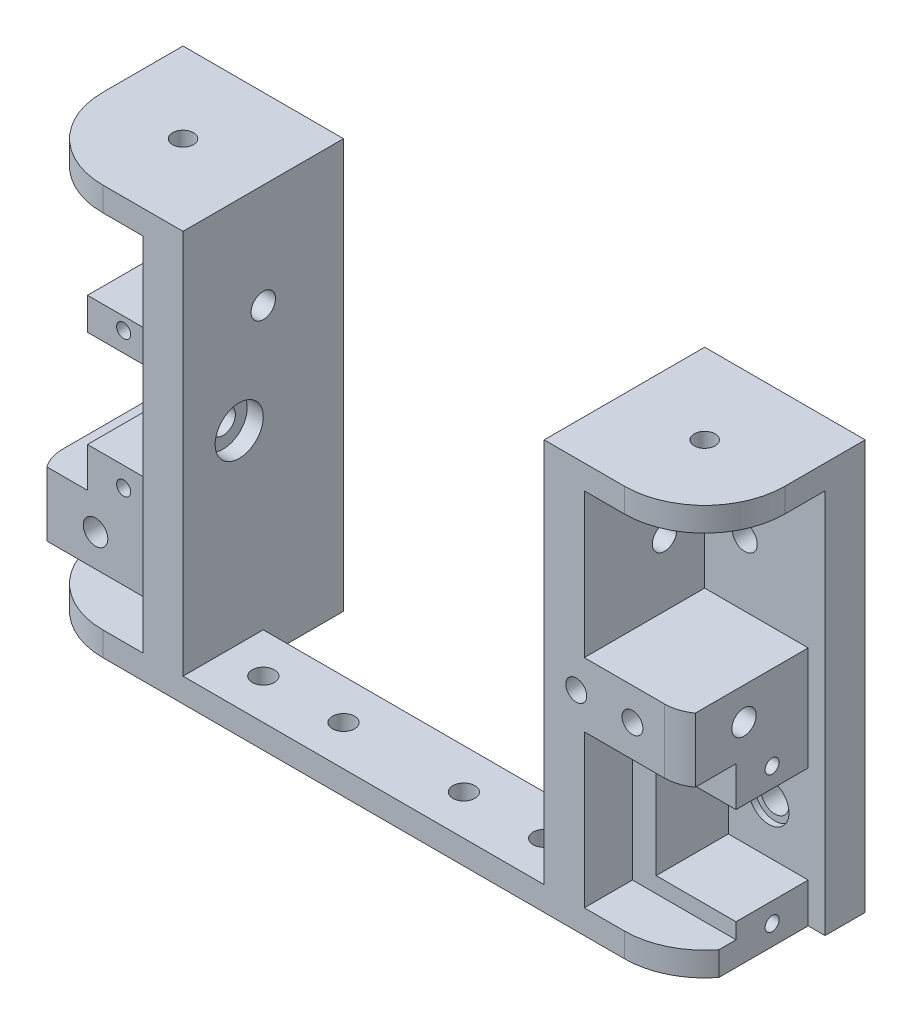
SolidWorks part; units mm, degrees
material "ABS"
ref_plane "Front Plane" through (0, 0, 0) normal (0, 0, 1) x (1, 0, 0)
ref_plane "Top Plane" through (0, 0, 0) normal (0, 1, 0) x (1, 0, 0)
ref_plane "Right Plane" through (0, 0, 0) normal (1, 0, 0) x (0, 0, -1)
sketch "Sketch1" plane through (0, 0, 0) normal (0, 0, 1) x (1, 0, 0)
  line L0 (-22.5, 7) -> (0, 7)
  line L1 (22.5, 7) -> (22.5, 45)
  line L2 (22.5, 45) -> (42.5, 45)
  line L3 (42.5, 45) -> (42.5, 0)
  line L4 (42.5, 0) -> (-42.5, 0)
  line L5 (-42.5, 0) -> (-42.5, 45)
  line L6 (-42.5, 45) -> (-22.5, 45)
  line L7 (-22.5, 45) -> (-22.5, 7)
  line L8 (-35.5, 39.9194) -> (-35.5, 0) construction
  line L9 (35.5, 39.9194) -> (35.5, 0) construction
  line L10 (0, 7) -> (0, 0) construction
  line L14 (0, 7) -> (22.5, 7)
  circle A0 centre (35.5, 8) radius 1.75
  circle A1 centre (-35.5, 8) radius 1.525
  circle A2 centre (32.5, 35) radius 1.55
  circle A3 centre (-32.5, 35) radius 1.55
  point P8 (0, 0)
  dimension "D3" = 3.5
  dimension "D10" = 3.1
  dimension "D11" = 3.05
  dimension "D1" = 71
  dimension "D2" = 22.5
  dimension "D4" = 8
  dimension "D5" = 7
  dimension "D6" = 7
  dimension "D7" = 45
  dimension "D8" = 35
  dimension "D9" = 3
extrude "main flange" add sketch "Sketch1" along normal blind 5
ref_plane "Plane1" through (22.5, 0, 0) normal (1, 0, 0) x (0, 0, -1)
sketch "Sketch2" plane through (22.5, 0, 0) normal (1, 0, 0) x (0, 0, -1)
  line L0 (-13, 45) -> (-13, 0) construction
  line L1 (-5, 45) -> (-20, 45)
  line L2 (-5, 45) -> (-5, 0)
  line L3 (-5, 0) -> (-20, 0)
  line L4 (-20, 45) -> (-20, 0)
  circle A0 centre (-13, 23) radius 1.525
  circle A1 centre (-10, 35) radius 1.525
  dimension "D2" = 3.05
  dimension "D5" = 3.05
  dimension "D1" = 15
  dimension "D3" = 23
  dimension "D4" = 13
  dimension "D6" = 35
  dimension "D7" = 3
extrude "side flange" add sketch "Sketch2" along normal blind 5
sketch "Sketch8" plane through (22.5, 0, 0) normal (-1, 0, 0) x (0, 0, 1)
  circle A0 centre (13, 23) radius 3
  dimension "D1" = 6
extrude "bearing cutout" [suppressed] cut sketch "Sketch8" against normal blind 2
mirror "Mirror1" about plane through (0, 0, 0) normal (1, 0, 0) of "side flange"
sketch "Sketch11" plane through (0, 0, 0) normal (0, -1, 0) x (1, 0, 0)
  line L0 (27.5, 20) -> (22.5, 20) construction
  line L1 (-42.5, 0) -> (42.5, 0)
  line L2 (-42.5, 0) -> (-42.5, 10)
  line L3 (-32.5, 20) -> (32.5, 20)
  line L4 (42.5, 0) -> (42.5, 10)
  arc A0 (32.5, 20) -> (42.5, 10) centre (32.5, 10) cw
  arc A1 (-42.5, 10) -> (-32.5, 20) centre (-32.5, 10) cw
  circle A2 centre (-32.5, 10) radius 1.3
  circle A3 centre (32.5, 10) radius 1.3
  dimension "D1" = 10
  dimension "D2" = 2.6
extrude "Boss-Extrude3" add sketch "Sketch11" along normal blind 3
sketch "Sketch12" plane through (0, 0, 0) normal (0, 1, 0) x (1, 0, 0)
  line L0 (-4, -3) -> (-4, 0)
  line L1 (22.5, 0) -> (-22.5, 0) construction
  line L2 (-4, 0) -> (4, 0)
  line L3 (4, 0) -> (4, -3)
  line L4 (0, 0) -> (0, -3) construction
  arc A0 (4, -3) -> (-4, -3) centre (0, -3) cw
  circle A1 centre (0, -3) radius 1.5 construction
  dimension "D2" = 8
  dimension "D3" = 3
  dimension "D1" = 3
extrude "Boss-Extrude4" add sketch "Sketch12" along normal up to surface (7 mm away) up to face at (5.625, 7, 3.125)
hole_wizard "CSK for M3 Flat Head Machine Screw1" positions "Sketch14" profile "Sketch15" countersink size "M3" standard "ANSI Metric" end condition up to next
sketch "Sketch14" plane through (0, -3, 0) normal (0, -1, 0) x (-1, 0, 0)
  line L0 (0, -3) -> (0, 0) construction
  point P0 (0, -3)
  dimension "D1" = 3
sketch "Sketch15" plane through (0, -3, 3) normal (1, 0, 0) x (0, 0, -1)
  line L0 (0, 0) -> (0, 10)
  line L1 (0, 10) -> (1.8, 10)
  line L2 (1.8, 10) -> (1.8, 1.5)
  line L3 (1.8, 1.5) -> (3.15, 0.15)
  line L4 (3.15, 0.15) -> (3.15, 0)
  line L6 (3.15, 0) -> (0, 0)
  line L7 (-1.8, 1.5) -> (-3.15, 0.15) construction
  line L11 (0, -6.35) -> (0, 107.95) construction
  dimension "Thru Hole Dia." = 3.6
  dimension "Thru Hole Depth" = 10
  dimension "C'Sink Dia." = 6.3
  dimension "C'Sink Angle" = 90
  dimension "Head Clearance" = 0.15
sketch "Sketch16" plane through (0, 45, 0) normal (0, 1, 0) x (1, 0, 0)
  line L0 (-22.5, 0) -> (-42.5, 0) construction
  line L1 (-42.5, 0) -> (-22.5, 0)
  line L2 (-42.5, 0) -> (-42.5, -10)
  line L3 (-32.5, -20) -> (-22.5, -20)
  line L4 (42.5, 0) -> (42.5, -10)
  line L5 (-42.5, -5) -> (-42.5, 0) construction
  line L6 (42.5, -5) -> (42.5, 0) construction
  line L7 (27.5, -20) -> (22.5, -20) construction
  line L8 (-22.5, 0) -> (-22.5, -20)
  line L9 (-22.5, -20) -> (-22.5, 0) construction
  line L10 (22.5, 0) -> (22.5, -20)
  line L11 (22.5, -20) -> (22.5, 0) construction
  line L12 (22.5, 0) -> (42.5, 0)
  line L13 (22.5, -20) -> (32.5, -20)
  arc A0 (-42.5, -10) -> (-32.5, -20) centre (-32.5, -10) ccw
  arc A1 (32.5, -20) -> (42.5, -10) centre (32.5, -10) ccw
  circle A2 centre (-32.5, -10) radius 1.3
  circle A3 centre (32.5, -10) radius 1.3
  dimension "D1" = 10
  dimension "D2" = 2.6
extrude "Top support" add sketch "Sketch16" along normal blind 3
sketch "Sketch18" plane through (27.5, 0, 0) normal (1, 0, 0) x (0, 0, -1)
  line L0 (-20, 45) -> (-20, 0) construction
  line L1 (-20, 27) -> (-5, 27)
  line L2 (-20, 27) -> (-20, 19)
  line L3 (-20, 19) -> (-5, 19)
  line L4 (-5, 27) -> (-5, 19)
  line L5 (-5, 0) -> (-5, 45) construction
  circle A0 centre (-13, 23) radius 1.525
  circle A1 centre (-13, 23) radius 1.525 construction
  dimension "D1" = 4
  dimension "D2" = 4
extrude "Boss-Extrude5" add sketch "Sketch18" along normal up to surface (15 mm away) up to face at (42.5, 19.6875, 5.9375)
sketch "Sketch19" plane through (0, 0, 5) normal (0, 0, 1) x (1, 0, 0)
  line L0 (-27.5, 45) -> (-27.5, 0) construction
  line L1 (-27.5, 12) -> (-42.5, 12)
  line L2 (-27.5, 12) -> (-27.5, 4)
  line L3 (-27.5, 4) -> (-42.5, 4)
  line L4 (-42.5, 12) -> (-42.5, 4)
  line L5 (-42.5, 45) -> (-42.5, 0) construction
  circle A0 centre (-35.5, 8) radius 1.525
  circle A1 centre (-35.5, 8) radius 1.525 construction
  dimension "D1" = 4
  dimension "D2" = 4
extrude "Boss-Extrude6" add sketch "Sketch19" along normal up to surface (15 mm away) up to face at (8.375, 27.35, 20)
fillet "Fillet1" radius 5 2 edges at (42.5, 23, 20) (-42.5, 8, 20)
hole_wizard "M3x0.5 Tapped Hole1" positions "Sketch21" profile "Sketch20" tap size "M3x0.5" standard "ANSI Metric"
sketch "Sketch21" plane through (-42.5, 0, 0) normal (-1, 0, 0) x (0, 0, 1)
  line L2 (15, 8) -> (4, 8) construction
  line L3 (0, 48) -> (0, -3) construction
  line L5 (15, 4) -> (15, 12) construction
  point P0 (11, 8)
  point P11 (4, 8)
  dimension "D1" = 4
  dimension "D3" = 7
sketch "Sketch20" plane through (-42.5, 8, 11) normal (0, 1, 0) x (0, 0, 1)
  line L0 (0, 0) -> (0, 8.2811)
  line L1 (0, 8.2811) -> (1.3, 7.5)
  line L2 (1.3, 7.5) -> (1.3, 0)
  line L5 (1.3, 0) -> (0, 0)
  line L10 (0, 8.2811) -> (-1.3, 7.5) construction
  line L11 (0, -6.35) -> (0, 107.95) construction
  dimension "Tap Drill Dia." = 2.6
  dimension "Tap Drill Depth" = 7.5
  dimension "Drill Angle" = 118
cosmetic thread "Hole Thread1" parameters "D1"=6, "D2"=3
cosmetic thread "Hole Thread2" parameters "D1"=6, "D2"=3
hole_wizard "M3x0.5 Tapped Hole2" positions "Sketch23" profile "Sketch22" tap size "M3x0.5" standard "ANSI Metric"
sketch "Sketch23" plane through (0, 0, 20) normal (0, 0, 1) x (1, 0, 0)
  line L0 (22.5, 23) -> (33.5, 23) construction
  line L1 (22.5, 48) -> (22.5, 0) construction
  line L5 (33.5, 23) -> (37.5, 23) construction
  line L6 (37.5, 19) -> (37.5, 27) construction
  point P0 (33.5, 23)
  point P2 (26.5, 23)
  dimension "D1" = 4
  dimension "D2" = 7
sketch "Sketch22" plane through (33.5, 23, 20) normal (1, 0, 0) x (0, -1, 0)
  line L0 (0, 0) -> (0, 8.2811)
  line L1 (0, 8.2811) -> (1.3, 7.5)
  line L2 (1.3, 7.5) -> (1.3, 0)
  line L5 (1.3, 0) -> (0, 0)
  line L10 (0, 8.2811) -> (-1.3, 7.5) construction
  line L11 (0, -6.35) -> (0, 107.95) construction
  dimension "Tap Drill Dia." = 2.6
  dimension "Tap Drill Depth" = 7.5
  dimension "Drill Angle" = 118
cosmetic thread "Hole Thread3" parameters "D1"=6, "D2"=3
cosmetic thread "Hole Thread4" parameters "D1"=6, "D2"=3
sketch "Sketch24" plane through (0, 0, 5) normal (0, 0, 1) x (1, 0, 0)
  circle A0 centre (35.5, 8) radius 2.5
  dimension "D1" = 5
extrude "Cut-Extrude1" cut sketch "Sketch24" against normal blind 0.75
sketch "Sketch25" plane through (-27.5, 0, 0) normal (-1, 0, 0) x (0, 0, 1)
  circle A0 centre (13, 23) radius 2.5
  dimension "D1" = 5
extrude "Cut-Extrude2" cut sketch "Sketch25" against normal blind 0.75
sketch "Sketch26" plane through (0, 7, 0) normal (0, 1, 0) x (1, 0, 0)
  line L0 (22.5, 0) -> (-22.5, 0) construction
  line L1 (-15.2, 0) -> (-5.2, 0)
  line L2 (-15.2, 0) -> (-15.2, -2.85)
  line L3 (-15.2, -2.85) -> (-5.2, -2.85)
  line L4 (-5.2, 0) -> (-5.2, -2.85)
  line L5 (0, 0) -> (0, 9.323) construction
  line L6 (5.2, 0) -> (5.2, -2.85)
  line L7 (15.2, -2.85) -> (5.2, -2.85)
  line L8 (15.2, 0) -> (15.2, -2.85)
  line L9 (15.2, 0) -> (5.2, 0)
  dimension "D1" = 5.2
  dimension "D2" = 2.85
  dimension "D3" = 10
extrude "Boss-Extrude7" add sketch "Sketch26" along normal blind 10
sketch "Sketch27" plane through (0, 0, 5) normal (0, 0, 1) x (1, 0, 0)
  line L0 (-27.5, 45) -> (-27.5, 12) construction
  line L1 (-27.5, 38) -> (-42.5, 38)
  line L2 (-27.5, 38) -> (-27.5, 32)
  line L3 (-27.5, 32) -> (-42.5, 32)
  line L4 (-42.5, 38) -> (-42.5, 32)
  line L5 (-42.5, 45) -> (-42.5, 12) construction
  line L6 (0, 0) -> (0, 39.7852) construction
  line L7 (-42.5, 35) -> (-32.5, 35) construction
  line L8 (42.5, 35) -> (32.5, 35) construction
  line L9 (42.5, 38) -> (42.5, 32)
  line L10 (27.5, 32) -> (42.5, 32)
  line L11 (27.5, 38) -> (27.5, 32)
  line L12 (27.5, 38) -> (42.5, 38)
  dimension "D1" = 6
sketch "Sketch30" plane through (0, 0, 0) normal (0, 1, 0) x (1, 0, 0)
  line L0 (-22.5, -20) -> (-22.5, -5) construction
  line L1 (-22.5, -5) -> (-3.4641, -5) construction
  line L2 (3.4641, -5) -> (22.5, -5) construction
  line L3 (22.5, -20) -> (22.5, -5) construction
  line L4 (22.5, -20) -> (-22.5, -20) construction
  line L5 (-22.5, -20) -> (-22.5, -5)
  line L6 (-22.5, -5) -> (-3.4641, -5)
  line L7 (3.4641, -5) -> (22.5, -5)
  line L8 (22.5, -20) -> (22.5, -5)
  line L9 (22.5, -20) -> (-22.5, -20)
  arc A0 (-3.4641, -5) -> (3.4641, -5) centre (0, -3) ccw construction
  arc A1 (-3.4641, -5) -> (3.4641, -5) centre (0, -3) ccw
extrude "Cut-Extrude3" [suppressed] cut sketch "Sketch30" against normal offset from surface (2 mm away) 1
sketch "Sketch31" [suppressed] plane through (0, 7, 0) normal (0, 1, 0) x (1, 0, 0)
  line L0 (22.5, -11) -> (22.5, 11) construction
  line L1 (-15.2, 0) -> (-22.5, 0)
  line L2 (-15.2, 0) -> (-15.2, -5)
  line L3 (-15.2, -5) -> (-22.5, -5)
  line L4 (-22.5, 0) -> (-22.5, -5)
  line L5 (15.2, 0) -> (22.5, 0)
  line L6 (15.2, 0) -> (15.2, -5)
  line L7 (15.2, -5) -> (22.5, -5)
  line L8 (22.5, 0) -> (22.5, -5)
  line L9 (3.4641, -5) -> (22.5, -5) construction
extrude "Cut-Extrude4" [suppressed] cut sketch "Sketch31" against normal blind 7
sketch "Sketch32" plane through (0, 0, 5) normal (0, 0, 1) x (1, 0, 0)
  line L0 (40.4, 14.05) -> (30.45, 14.05)
  line L2 (30.45, 14.05) -> (30.45, 1.95)
  line L3 (30.45, 1.95) -> (40.4, 1.95)
  line L4 (40.4, 1.95) -> (40.4, 0)
  line L5 (40.4, 0) -> (27.5, 0)
  line L6 (27.5, 0) -> (27.5, 19) construction
  line L7 (27.5, 0) -> (42.5, 0) construction
  line L8 (27.5, 0) -> (27.5, 19)
  line L9 (27.5, 19) -> (40.4, 19)
  line L10 (40.4, 19) -> (40.4, 14.05)
  line L11 (35.5, 8) -> (30.45, 8) construction
  line L12 (37.5, 19) -> (27.5, 19) construction
  dimension "D1" = 12.1
  dimension "D2" = 5.05
  dimension "D3" = 4.9
extrude "Motor mount" add sketch "Sketch32" along normal blind 9
sketch "Sketch33" plane through (42.5, 0, 0) normal (1, 0, 0) x (0, 0, -1)
  line L0 (-15, 27) -> (-5, 27) construction
  line L1 (-20, -3) -> (-5, -3)
  line L2 (-20, -3) -> (-20, 27)
  line L3 (-20, 27) -> (-5, 27)
  line L4 (-5, -3) -> (-5, 27)
  line L5 (-20, -3) -> (-5, 27) construction
  line L6 (-20, 27) -> (-5, -3) construction
  line L7 (-5, 0) -> (-5, 19) construction
  line L8 (0, -3) -> (-10, -3) construction
  line L9 (-20, 19) -> (-20, 27) construction
  point P0 (-12.5, 12)
extrude "Cut-Extrude6" cut sketch "Sketch33" against normal up to surface (2.1 mm away) up to face at (40.4, 16.525, 9.5)
sketch "Sketch34" plane through (40.4, 0, 0) normal (1, 0, 0) x (0, 0, -1)
  line L0 (-9.5, 16.5) -> (-9.5, 14.05) construction
  line L1 (-14, 14.05) -> (-5, 14.05) construction
  line L2 (-9.5, 14.05) -> (-9.5, 1.95) construction
  line L3 (-14, 1.95) -> (-5, 1.95) construction
  line L4 (-9.5, 1.95) -> (-9.5, -3) construction
  line L5 (-16.1311, -3) -> (-5, -3) construction
  line L7 (-9.5, 8) -> (-14.7798, 8) construction
  circle A0 centre (-9.5, 16.5) radius 0.875
  circle A1 centre (-9.5, -0.5) radius 0.875
  dimension "D1" = 1.75
  dimension "D2" = 17
  dimension "D3" = 8.5
extrude "Cut-Extrude7" cut sketch "Sketch34" against normal blind 7
sketch "Sketch35" plane through (-27.5, 0, 0) normal (-1, 0, 0) x (0, 0, 1)
  line L0 (13, 23) -> (20, 23) construction
  line L1 (20, 45) -> (20, 12) construction
  line L2 (20, 29.05) -> (7.95, 29.05)
  line L3 (7.95, 29.05) -> (7.95, 16.95)
  line L4 (7.95, 16.95) -> (20, 16.95)
  line L5 (20, 16.95) -> (20, 12)
  line L6 (20, 12) -> (5, 12)
  line L7 (5, 12) -> (5, 33.05)
  line L8 (5, 33.05) -> (20, 33.05)
  line L9 (20, 33.05) -> (20, 29.05)
  line L10 (13, 23) -> (7.95, 23) construction
  dimension "D1" = 5.05
  dimension "D2" = 12.1
  dimension "D3" = 4
extrude "Boss-Extrude9" add sketch "Sketch35" along normal blind 9
sketch "Sketch36" plane through (0, 0, 20) normal (0, 0, 1) x (1, 0, 0)
  line L0 (-42.5, 45) -> (-42.5, 12) construction
  line L1 (-27.5, 33.05) -> (-42.5, 33.05)
  line L2 (-27.5, 33.05) -> (-27.5, 4)
  line L3 (-27.5, 4) -> (-42.5, 4)
  line L4 (-42.5, 33.05) -> (-42.5, 4)
extrude "Cut-Extrude8" cut sketch "Sketch36" against normal blind 2.1
sketch "Sketch37" plane through (0, 0, 17.9) normal (0, 0, 1) x (1, 0, 0)
  line L0 (-32, 16.95) -> (-32, 29.05) construction
  line L1 (-36.5, 16.95) -> (-27.5, 16.95) construction
  line L2 (-27.5, 29.05) -> (-36.5, 29.05) construction
  line L3 (-32, 23) -> (-29.1995, 23) construction
  line L4 (-32, 31.5) -> (-32, 29.05) construction
  circle A0 centre (-32, 31.5) radius 0.875
  circle A1 centre (-32, 14.5) radius 0.875
  dimension "D1" = 1.75
  dimension "D2" = 8.5
  dimension "D3" = 8.5
extrude "Cut-Extrude9" cut sketch "Sketch37" against normal blind 7
sketch "Sketch38" [suppressed] plane through (0, -3, 0) normal (0, -1, 0) x (1, 0, 0)
  line L0 (22.5, -11) -> (22.5, 11) construction
  line L1 (-22.5, 0) -> (22.5, 0)
  line L2 (-22.5, 0) -> (-22.5, 10)
  line L3 (-22.5, 10) -> (22.5, 10)
  line L4 (22.5, 0) -> (22.5, 10)
  line L5 (32.5, 20) -> (-32.5, 20) construction
  dimension "D1" = 10
sketch "Sketch39" plane through (0, -3, 0) normal (0, -1, 0) x (1, 0, 0)
  line L0 (22.5, -11) -> (22.5, 11) construction
  line L1 (-22.5, 0) -> (22.5, 0)
  line L2 (-22.5, 0) -> (-22.5, 10)
  line L3 (-22.5, 10) -> (22.5, 10)
  line L4 (22.5, 0) -> (22.5, 10)
  line L5 (32.5, 20) -> (-32.5, 20) construction
  dimension "D1" = 10
extrude "Cut-Extrude11" cut sketch "Sketch39" against normal through all
sketch "Sketch40" plane through (0, 0, 0) normal (0, 1, 0) x (1, 0, 0)
  line L0 (0, 0) -> (0, -20) construction
  line L1 (22.5, -20) -> (-22.5, -20) construction
  line L2 (0, -15) -> (-21.4186, -15) construction
  circle A0 centre (-17.5, -15) radius 1.375
  circle A1 centre (-7.5, -15) radius 1.375
  circle A2 centre (7.5, -15) radius 1.375
  circle A3 centre (17.5, -15) radius 1.375
  dimension "D1" = 2.75
  dimension "D2" = 7.5
  dimension "D3" = 10
  dimension "D4" = 5
extrude "Mount Holes" cut sketch "Sketch40" against normal through all
sketch "Sketch41" plane through (-22.5, 0, 0) normal (1, 0, 0) x (0, 0, -1)
  circle A0 centre (-13, 23) radius 3
  dimension "D1" = 6
extrude "Bearing Holder" cut sketch "Sketch41" against normal blind 2
sketch "Sketch42" plane through (0, 0, 0) normal (0, 0, -1) x (-1, 0, 0)
  circle A0 centre (-35.5, 8) radius 3
  dimension "D1" = 6
extrude "Cut-Extrude14" cut sketch "Sketch42" against normal blind 2
equation "\"clearance\"= 0.2mm'3D printed hole"
equation "\"tight\"= - 0.2mm'3D printed hole"
